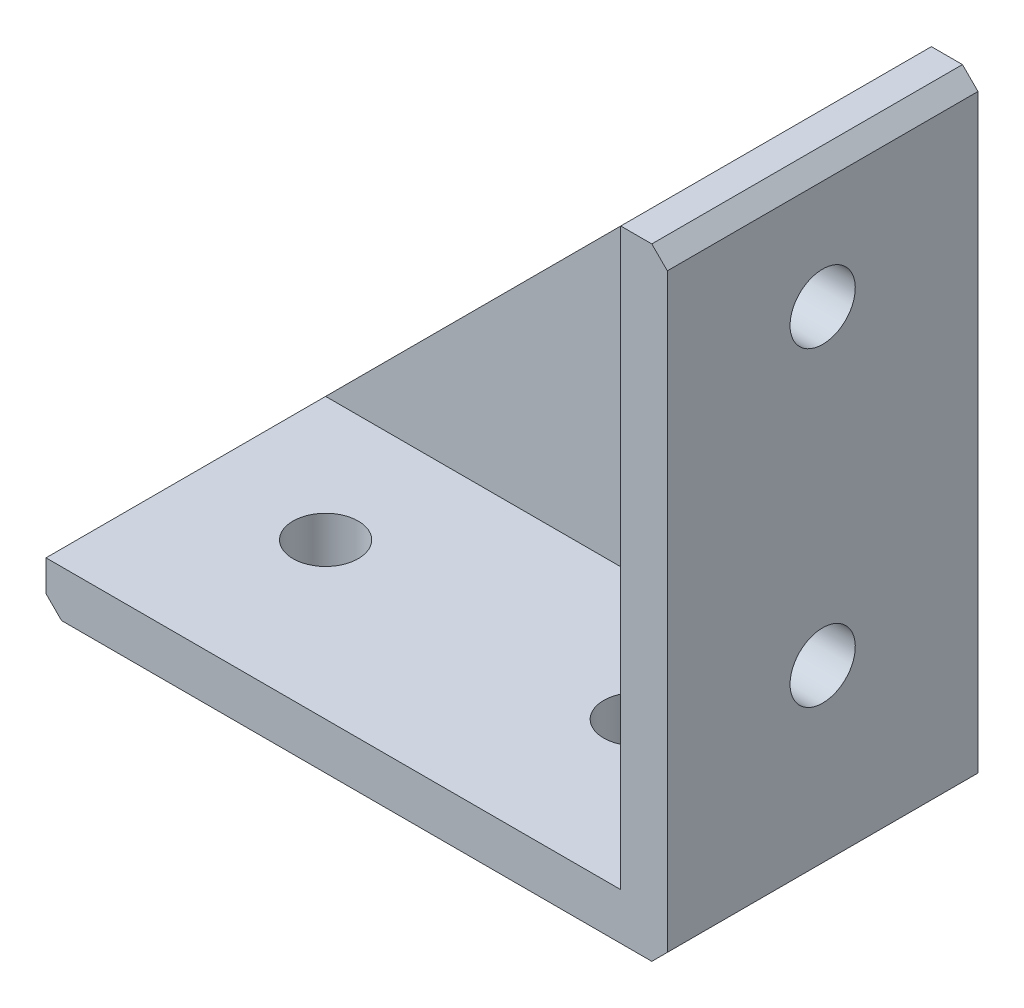
SolidWorks part; units mm, degrees
ref_plane "Plan de face" through (0, 0, 0) normal (0, 0, 1) x (1, 0, 0)
ref_plane "Plan de dessus" through (0, 0, 0) normal (0, 1, 0) x (1, 0, 0)
ref_plane "Plan de droite" through (0, 0, 0) normal (1, 0, 0) x (0, 0, -1)
sketch "Esquisse1" plane through (0, 0, 0) normal (0, 0, 1) x (1, 0, 0)
  line L1 (0, 0) -> (-40, 0)
  line L2 (0, 0) -> (0, 40)
  line L3 (0, 40) -> (-40, 40)
  line L4 (-40, 0) -> (-40, 40)
  dimension "D1" = 40
  dimension "D2" = 40
extrude "Boss.-Extru.1" add sketch "Esquisse1" along normal blind 20
sketch "Esquisse2" plane through (0, 0, 20) normal (0, 0, 1) x (1, 0, 0)
  line L0 (0, 0) -> (0, 40) construction
  line L1 (-40, 40) -> (-3, 40)
  line L2 (-40, 40) -> (-40, 3)
  line L3 (-40, 3) -> (-3, 3)
  line L4 (-3, 40) -> (-3, 3)
  line L5 (-40, 0) -> (0, 0) construction
  dimension "D1" = 3
  dimension "D2" = 3
extrude "Enlèv. mat.-Extru.1" cut sketch "Esquisse2" against normal blind 18
sketch "Esquisse3" plane through (0, 0, 2) normal (0, 0, 1) x (1, 0, 0)
  line L0 (-40, 3) -> (-3, 40)
  line L1 (-3, 40) -> (-40, 40)
  line L2 (-40, 40) -> (-40, 3)
extrude "Enlèv. mat.-Extru.2" cut sketch "Esquisse3" against normal through all
chamfer "Chanfrein1" distance 1 angle 45 3 edges at (0, 0, 10) (-40, 0, 10) (0, 40, 10)
sketch "Esquisse4" plane through (0, 3, 0) normal (0, 1, 0) x (1, 0, 0)
  line L0 (-40, -2) -> (-40, -20) construction
  line L1 (-40, -20) -> (-3, -20) construction
  circle A0 centre (-12, -10) radius 2.1
  circle A1 centre (-32, -10) radius 2.1
  dimension "D1" = 4.2
  dimension "D2" = 4.2
  dimension "D3" = 20
  dimension "D4" = 8
  dimension "D5" = 10
  dimension "D6" = 10
extrude "Enlèv. mat.-Extru.3" cut sketch "Esquisse4" against normal through all
sketch "Esquisse5" plane through (-3, 0, 0) normal (-1, 0, 0) x (0, 0, 1)
  line L0 (2, 40) -> (20, 40) construction
  line L2 (20, 3) -> (20, 40) construction
  circle A0 centre (10, 12) radius 2.1
  circle A1 centre (10, 32) radius 2.1
  point P8 (20, 37.2057)
  dimension "D1" = 4.2
  dimension "D2" = 4.2
  dimension "D3" = 20
  dimension "D4" = 8
  dimension "D5" = 10
  dimension "D6" = 10
extrude "Enlèv. mat.-Extru.4" cut sketch "Esquisse5" against normal through all
